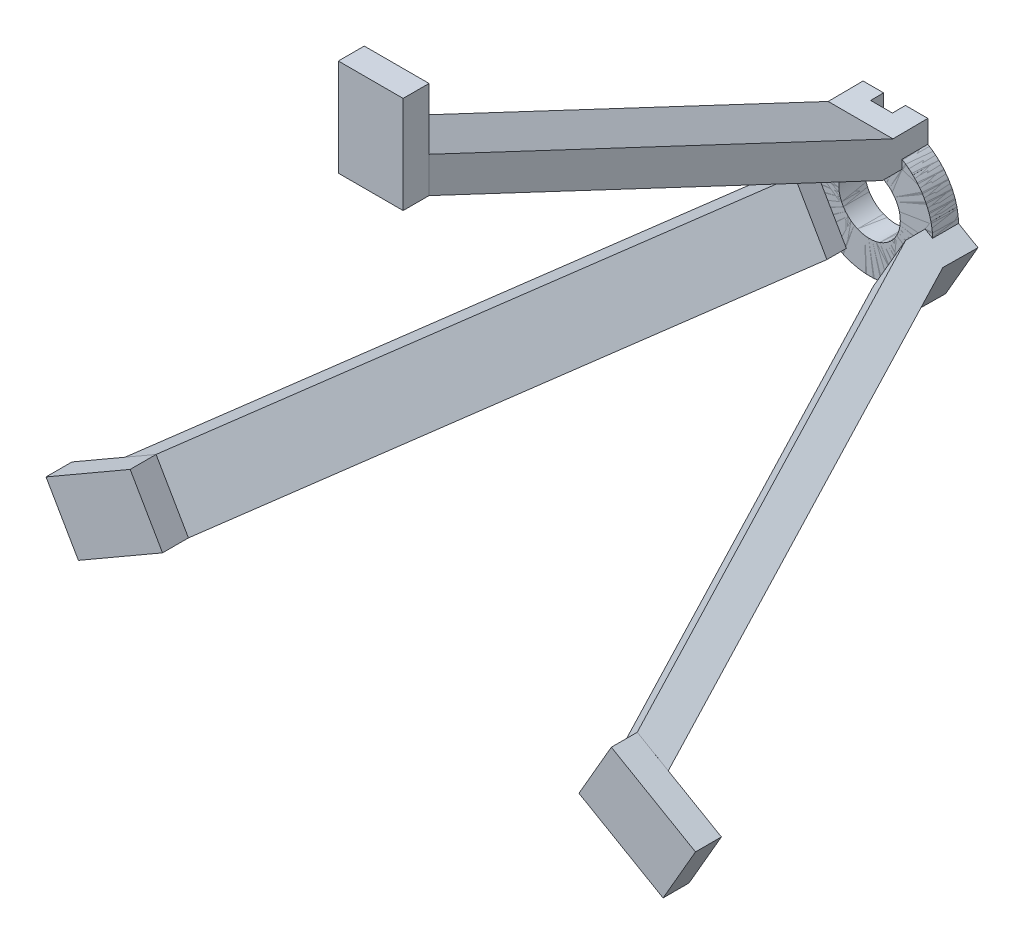
SolidWorks part; units mm, degrees
ref_plane "Front Plane" through (0, 0, 0) normal (0, 0, 1) x (1, 0, 0)
ref_plane "Top Plane" through (0, 0, 0) normal (0, 1, 0) x (1, 0, 0)
ref_plane "Right Plane" through (0, 0, 0) normal (1, 0, 0) x (0, 0, -1)
sketch "Sketch1" plane through (0, 0, 0) normal (0, 0, 1) x (1, 0, 0)
  line L0 (-6.6908, 7.0919) -> (6.6908, 7.0919)
  circle A0 centre (0, 0) radius 4.75
  circle A1 centre (0, 0) radius 9.75
  dimension "D1" = 9.5
  dimension "D2" = 19.5
extrude "Boss-Extrude1" add sketch "Sketch1" along normal blind 4 contours L0 A1 A0
sketch "Sketch2" plane through (0, 0, 4) normal (0, 0, 1) x (1, 0, 0)
  line L0 (0, 0) -> (0, 13.0507) construction
  line L1 (-5, 7.0173) -> (5, 7.0173)
  line L2 (-5, 7.0173) -> (-5, 10.287)
  line L3 (-5, 10.287) -> (5, 10.287)
  line L4 (5, 7.0173) -> (5, 10.287)
  dimension "D1" = 10
  dimension "D2" = 5
extrude "Boss-Extrude3" add sketch "Sketch2" along normal blind 3 and the other way blind 2
ref_plane "Plane2" through (0, 0, 81) normal (0, 0, 1) x (1, 0, 0)
sketch "Sketch6" plane through (0, 0, 81) normal (0, 0, 1) x (1, 0, 0)
  line L0 (0, 0) -> (0, 77.9527) construction
  line L1 (-5, 55) -> (5, 55)
  line L2 (-5, 55) -> (-5, 40)
  line L3 (-5, 40) -> (5, 40)
  line L4 (5, 55) -> (5, 40)
  line L5 (0, 0) -> (35.0232, 0) construction
  line L6 (0, 0) -> (-42.3784, 0) construction
  dimension "D1" = 40
  dimension "D2" = 15
  dimension "D3" = 5
  dimension "D4" = 10
extrude "Boss-Extrude4" add sketch "Sketch6" against normal blind 4 separate body
ref_plane "Plane3" through (-5, 0, 0) normal (-1, 0, 0) x (0, 0, 1)
sketch "Sketch7" plane through (-5, 0, 0) normal (-1, 0, 0) x (0, 0, 1)
  line L0 (77, 40) -> (7, 7.0173)
  line L1 (76.9966, 45.5256) -> (5.3857, 11.7839)
  line L2 (0, 7.0173) -> (0, 11.8285)
  line L3 (76.9966, 45.5256) -> (77, 40)
  line L4 (0, 11.8285) -> (5.3857, 11.7839)
  line L5 (0, 7.0173) -> (7, 7.0173)
  dimension "D1" = 5
extrude "Boss-Extrude5" add sketch "Sketch7" against normal blind 10
pattern_circular "CirPattern1" count 3 over 360 about axis through (0, 0, 0) along (0, 0, 1) of bodies 105 106
sketch "Sketch8" plane through (0, 0, 0) normal (0, 0, -1) x (-1, 0, 0)
  line L1 (-1.5382, 12.1776) -> (1.8294, 12.1776)
  line L2 (-1.5382, 12.1776) -> (-1.5382, 6.9513)
  line L3 (-1.5382, 6.9513) -> (1.8294, 6.9513)
  line L4 (1.8294, 12.1776) -> (1.8294, 6.9513)
extrude "Cut-Extrude1" cut sketch "Sketch8" against normal blind 2
